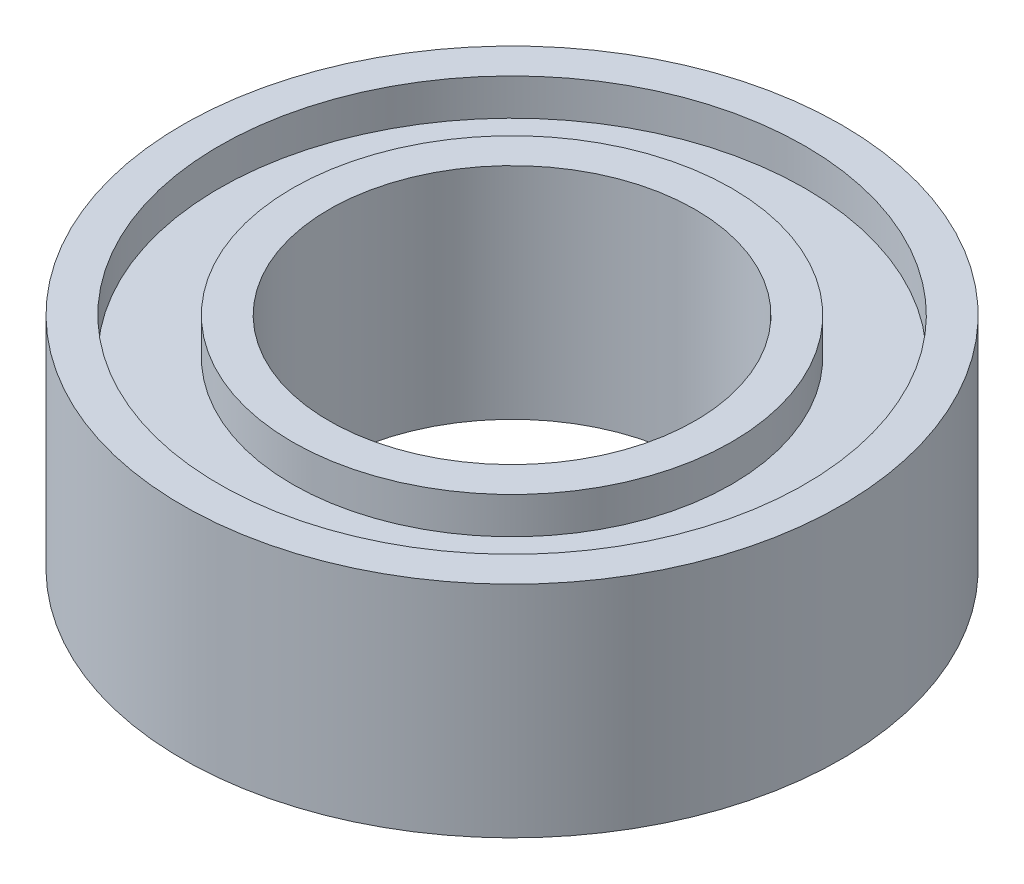
SolidWorks part; units mm, degrees
ref_plane "Front Plane" through (0, 0, 0) normal (0, 0, 1) x (1, 0, 0)
ref_plane "Top Plane" through (0, 0, 0) normal (0, 1, 0) x (1, 0, 0)
ref_plane "Right Plane" through (0, 0, 0) normal (1, 0, 0) x (0, 0, -1)
sketch "Sketch1" plane through (0, 0, 0) normal (0, 0, 1) x (1, 0, 0)
  line L0 (-2.5, 2.5) -> (-3, 2.5)
  line L1 (-3, 2.5) -> (-3, 2)
  line L2 (-3, 2) -> (-4, 2)
  line L3 (-4, 2) -> (-4, 2.5)
  line L4 (-4, 2.5) -> (-4.5, 2.5)
  line L5 (-4.5, 2.5) -> (-4.5, -0.5)
  line L6 (-4.5, -0.5) -> (-4, -0.5)
  line L7 (-4, -0.5) -> (-4, 0)
  line L8 (-4, 0) -> (-3, 0)
  line L9 (-3, 0) -> (-3, -0.5)
  line L10 (-3, -0.5) -> (-2.5, -0.5)
  line L11 (0, 0) -> (0, 9.4844) construction
  line L12 (-2.5, -0.5) -> (-2.5, 2.5)
  dimension "D1" = 4.5
  dimension "D2" = 2.5
  dimension "D3" = 0.5
  dimension "D5" = 3
revolve "Revolve1" add sketch "Sketch1" angle 360 about L11
equation "\"D_hull\"= 5"
equation "\"D\"= 9"
equation "\"tykkelse\"= 3"
equation "\"D2@Sketch1\"=\"D_hull\"/2"
equation "\"D1@Sketch1\"=\"D\"/2"
equation "\"D5@Sketch1\"=\"tykkelse\""
equation "\"D3@Sketch1\"=0.5"
